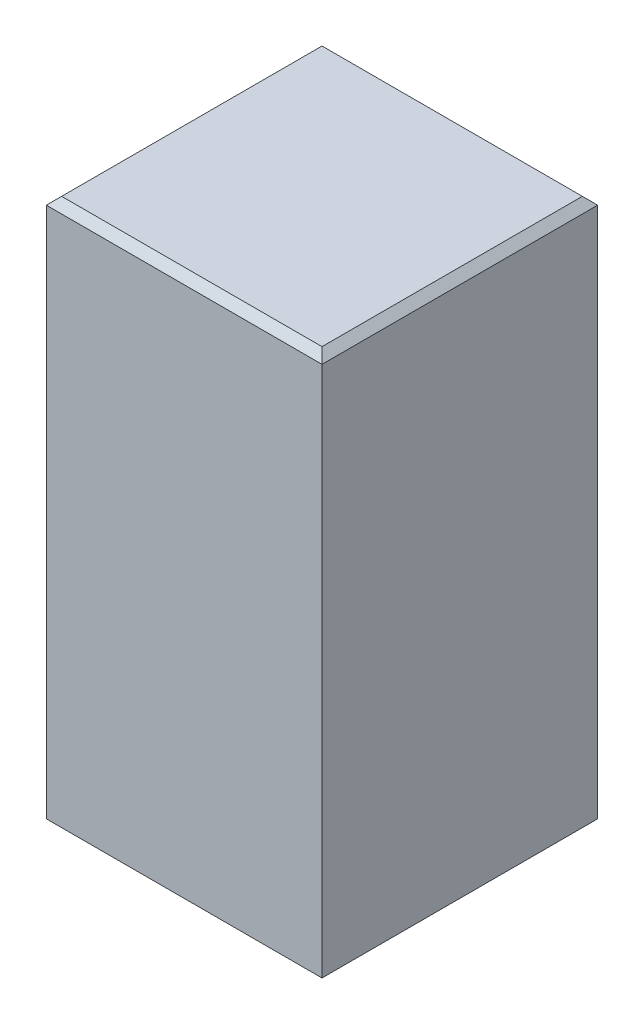
SolidWorks part; units mm, degrees
ref_plane "Front Plane" through (0, 0, 0) normal (0, 0, 1) x (1, 0, 0)
ref_plane "Top Plane" through (0, 0, 0) normal (0, 1, 0) x (1, 0, 0)
ref_plane "Right Plane" through (0, 0, 0) normal (1, 0, 0) x (0, 0, -1)
sketch "Sketch1" plane through (0, 0, 0) normal (0, 1, 0) x (1, 0, 0)
  line L0 (0, 29.8985) -> (0, -22.8338) construction
  line L1 (-8.2, 8.2) -> (8.2, 8.2)
  line L2 (-8.2, 8.2) -> (-8.2, -8.2)
  line L3 (-8.2, -8.2) -> (8.2, -8.2)
  line L4 (8.2, 8.2) -> (8.2, -8.2)
  line L5 (-9, 9) -> (9, 9)
  line L6 (-9, 9) -> (-9, -9)
  line L7 (-9, -9) -> (9, -9)
  line L8 (9, 9) -> (9, -9)
  line L9 (-32.4215, 0) -> (43.2708, 0) construction
  dimension "D1" = 16.4
  dimension "D2" = 16.4
  dimension "D3" = 0.8
  dimension "D4" = 0.8
extrude "Boss-Extrude1" add sketch "Sketch1" along normal blind 34
sketch "Sketch2" plane through (0, 34, 0) normal (0, 1, 0) x (1, 0, 0)
  line L1 (-9, 9) -> (9, 9)
  line L2 (-9, 9) -> (-9, -9)
  line L3 (-9, -9) -> (9, -9)
  line L4 (9, 9) -> (9, -9)
extrude "Boss-Extrude2" add sketch "Sketch2" along normal blind 1.2
chamfer "Chamfer1" distance 0.5 angle 45 4 edges at (-9, 35.2, 0) (0, 35.2, -9) (9, 35.2, 0) (0, 35.2, 9)
